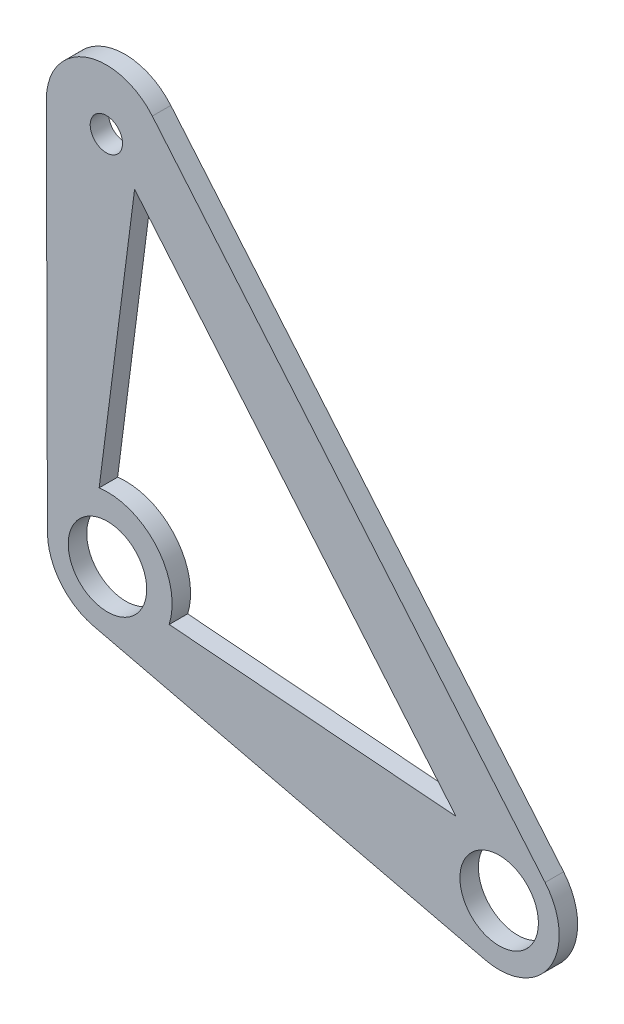
SolidWorks part; units mm, degrees
ref_plane "前视基准面" through (0, 0, 0) normal (0, 0, 1) x (1, 0, 0)
ref_plane "上视基准面" through (0, 0, 0) normal (0, 1, 0) x (1, 0, 0)
ref_plane "右视基准面" through (0, 0, 0) normal (1, 0, 0) x (0, 0, -1)
sketch "草图1" plane through (0, 0, 0) normal (0, 0, 1) x (1, 0, 0)
  line L0 (0, 0) -> (42.4143, -10.0989) construction
  line L1 (-0.1178, 40.4998) -> (0, 0) construction
  line L2 (-0.1178, 40.4998) -> (42.4143, -10.0989) construction
  line L3 (-6.5, -0.0189) -> (-6.6178, 40.4809)
  line L4 (-1.5056, -6.3232) -> (40.9087, -16.4221)
  line L5 (4.8578, 44.6823) -> (47.39, -5.9164)
  circle A0 centre (0, 0) radius 4.25
  circle A1 centre (42.4143, -10.0989) radius 4.25
  circle A2 centre (-0.1178, 40.4998) radius 1.75
  circle A3 centre (0, 0) radius 6.5
  circle A4 centre (-0.1178, 40.4998) radius 6.5
  circle A5 centre (42.4143, -10.0989) radius 6.5
  point P15 (21.1482, 15.2005)
  dimension "D3" = 3.5
  dimension "D4" = 8.5
  dimension "D5" = 8.5
  dimension "D6" = 13
  dimension "D7" = 13
  dimension "D8" = 13
  dimension "D1" = 43.6
  dimension "D2" = 40.5
  dimension "D9" = 66.1
extrude "凸台-拉伸1" add sketch "草图1" along normal blind 2
sketch "草图2" plane through (0, 0, 2) normal (0, 0, 1) x (1, 0, 0)
  line L0 (-0.1178, 40.4998) -> (42.4143, -10.0989) construction
  line L1 (2.9386, 36.8638) -> (37.7493, -4.5491)
  line L3 (2.9386, 36.8638) -> (-0.8997, 6.9419)
  line L4 (-0.8997, 6.9419) -> (6.6839, -2.0799) construction
  line L5 (6.6839, -2.0799) -> (37.7493, -4.5491)
  circle A0 centre (-0.1178, 40.4998) radius 1.75 construction
  circle A1 centre (-0.1178, 40.4998) radius 1.75
  circle A2 centre (42.4143, -10.0989) radius 4.25 construction
  circle A3 centre (42.4143, -10.0989) radius 4.25
  arc A4 (6.6839, -2.0799) -> (-0.8997, 6.9419) centre (0, 0) ccw
  dimension "D1" = 14
  dimension "D2" = 4.75
  dimension "D3" = 7.25
extrude "切除-拉伸1" cut sketch "草图2" against normal through all contours A3 | A4 L3 L1 L5
